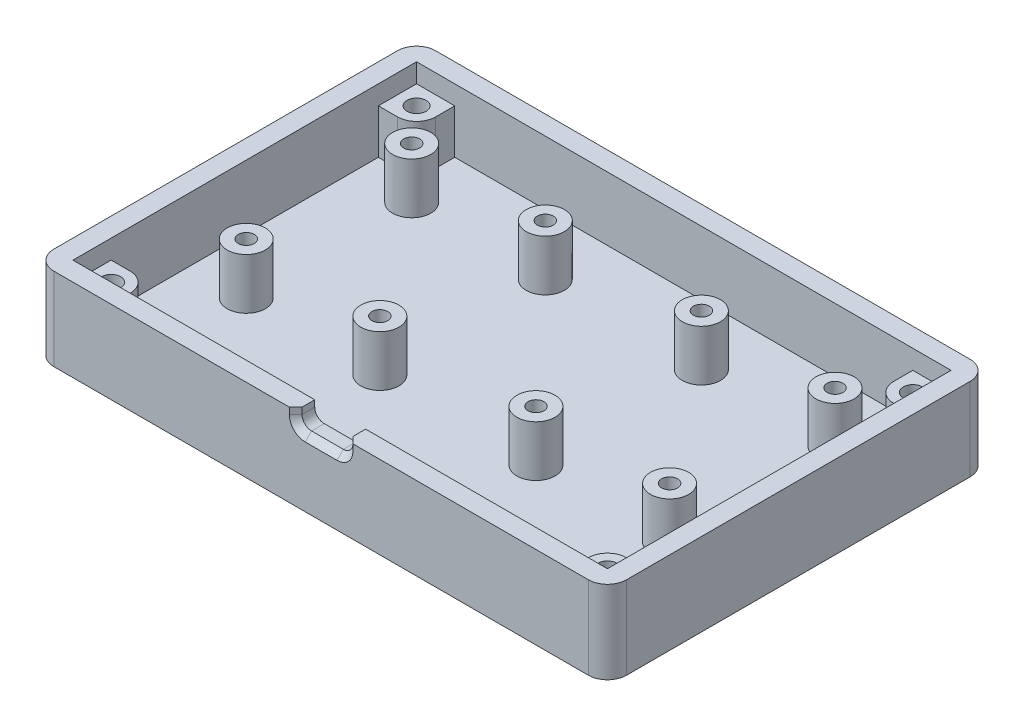
SolidWorks part; units mm, degrees
ref_plane "Спереди" through (0, 0, 0) normal (0, 0, 1) x (1, 0, 0)
ref_plane "Сверху" through (0, 0, 0) normal (0, 1, 0) x (1, 0, 0)
ref_plane "Справа" through (0, 0, 0) normal (1, 0, 0) x (0, 0, -1)
other "Configuration Table"
sketch "Эскиз2" plane through (0, 0, 0) normal (0, 1, 0) x (1, 0, 0)
  line L0 (-48.2034, 25.4414) -> (41.7966, 25.4414)
  line L1 (41.7966, 25.4414) -> (41.7966, -34.5586)
  line L2 (41.7966, -34.5586) -> (-48.2034, -34.5586)
  line L3 (-48.2034, -34.5586) -> (-48.2034, 25.4414)
  dimension "D1" = 90
  dimension "D2" = 60
extrude "Бобышка-Вытянуть1" add sketch "Эскиз2" along normal blind 3
sketch "Эскиз4" plane through (0, 3, 0) normal (0, 1, 0) x (1, 0, 0)
  line L0 (-3.2034, 25.4414) -> (-3.2034, -34.5586) construction
  line L1 (41.7966, 25.4414) -> (-48.2034, 25.4414) construction
  line L2 (-48.2034, -34.5586) -> (41.7966, -34.5586) construction
  line L3 (-48.2034, -4.5586) -> (41.7966, -4.5586) construction
  line L4 (-48.2034, 25.4414) -> (-48.2034, -34.5586) construction
  line L5 (41.7966, -34.5586) -> (41.7966, 25.4414) construction
  line L6 (-38.9685, 15.4414) -> (-12.9685, 15.4414) construction
  line L7 (-12.9685, 15.4414) -> (-12.9685, -18.0586) construction
  line L8 (-12.9685, -18.0586) -> (-38.9685, -18.0586) construction
  line L9 (-38.9685, -18.0586) -> (-38.9685, 15.4414) construction
  line L10 (-42.2034, 19.4414) -> (35.7966, 19.4414) construction
  line L11 (35.7966, 19.4414) -> (35.7966, -28.5586) construction
  line L12 (35.7966, -28.5586) -> (-42.2034, -28.5586) construction
  line L13 (-42.2034, -28.5586) -> (-42.2034, 19.4414) construction
  line L14 (32.5616, -18.0586) -> (32.5616, 15.4414) construction
  line L15 (6.5616, -18.0586) -> (32.5616, -18.0586) construction
  line L16 (6.5616, 15.4414) -> (6.5616, -18.0586) construction
  line L17 (32.5616, 15.4414) -> (6.5616, 15.4414) construction
  line L18 (-25.9685, 15.4414) -> (-25.9685, -18.0586) construction
  line L19 (-38.9685, -0.0586) -> (-12.9685, -0.0586) construction
  circle A0 centre (-36.4685, 12.9414) radius 3
  circle A1 centre (-36.4685, 12.9414) radius 1.25
  circle A2 centre (-15.4685, 12.9414) radius 1.25
  circle A3 centre (-15.4685, 12.9414) radius 3
  circle A4 centre (-15.4685, -13.0586) radius 3
  circle A5 centre (-15.4685, -13.0586) radius 1.25
  circle A6 centre (-36.4685, -13.0586) radius 1.25
  circle A7 centre (-36.4685, -13.0586) radius 3
  circle A8 centre (9.0616, -13.0586) radius 1.25
  circle A9 centre (9.0616, -13.0586) radius 3
  circle A10 centre (30.0616, -13.0586) radius 3
  circle A11 centre (30.0616, -13.0586) radius 1.25
  circle A12 centre (9.0616, 12.9414) radius 3
  circle A13 centre (9.0616, 12.9414) radius 1.25
  circle A14 centre (30.0616, 12.9414) radius 1.25
  circle A15 centre (30.0616, 12.9414) radius 3
  dimension "D10" = 6
  dimension "D11" = 2.5
  dimension "D1" = 6
  dimension "D2" = 6
  dimension "D3" = 6
  dimension "D4" = 6
  dimension "D5" = 26
  dimension "D6" = 33.5
  dimension "D7" = 20
  dimension "D8" = 2.5
  dimension "D9" = 2.5
  dimension "D12" = 13
  dimension "D13" = 5
  dimension "D14" = 13
extrude "Бобышка-Вытянуть2" add sketch "Эскиз4" along normal blind 8
sketch "Эскиз5" plane through (0, 3, 0) normal (0, 1, 0) x (1, 0, 0)
  line L0 (-45.2034, 22.4414) -> (-45.2034, -31.5586)
  line L1 (-45.2034, -31.5586) -> (38.7966, -31.5586)
  line L2 (38.7966, -31.5586) -> (38.7966, 22.4414)
  line L3 (38.7966, 22.4414) -> (-45.2034, 22.4414)
  line L4 (41.7966, 25.4414) -> (-48.2034, 25.4414) construction
  line L5 (-48.2034, 25.4414) -> (-48.2034, -34.5586) construction
  line L6 (-48.2034, -34.5586) -> (41.7966, -34.5586) construction
  line L7 (41.7966, -34.5586) -> (41.7966, 25.4414) construction
  line L9 (-48.2034, 25.4414) -> (41.7966, 25.4414)
  line L10 (-48.2034, 25.4414) -> (-48.2034, -34.5586)
  line L11 (-48.2034, -34.5586) -> (41.7966, -34.5586)
  line L12 (41.7966, 25.4414) -> (41.7966, -34.5586)
  dimension "D1" = 3
  dimension "D2" = 3
  dimension "D3" = 3
  dimension "D4" = 3
extrude "Бобышка-Вытянуть3" add sketch "Эскиз5" along normal blind 10
sketch "Эскиз7" plane through (0, 3, 0) normal (0, 1, 0) x (1, 0, 0)
  line L0 (-39.2034, 19.4414) -> (-39.2034, 22.4414)
  line L1 (38.7966, 22.4414) -> (-45.2034, 22.4414) construction
  line L2 (-42.2034, 16.4414) -> (-45.2034, 16.4414)
  line L3 (-45.2034, 22.4414) -> (-45.2034, -31.5586) construction
  line L4 (-45.2034, 16.4414) -> (-45.2034, 22.4414)
  line L5 (-45.2034, 22.4414) -> (-39.2034, 22.4414)
  line L6 (-3.2034, 22.4414) -> (-3.2034, -31.5586) construction
  line L7 (38.7966, 22.4414) -> (-45.2034, 22.4414) construction
  line L8 (-45.2034, -31.5586) -> (38.7966, -31.5586) construction
  line L9 (-45.2034, -4.5586) -> (38.7966, -4.5586) construction
  line L10 (38.7966, -31.5586) -> (38.7966, 22.4414) construction
  line L11 (38.7966, 22.4414) -> (32.7966, 22.4414)
  line L12 (38.7966, 16.4414) -> (38.7966, 22.4414)
  line L13 (35.7966, 16.4414) -> (38.7966, 16.4414)
  line L14 (32.7966, 19.4414) -> (32.7966, 22.4414)
  line L15 (32.7966, -28.5586) -> (32.7966, -31.5586)
  line L16 (35.7966, -25.5586) -> (38.7966, -25.5586)
  line L17 (38.7966, -25.5586) -> (38.7966, -31.5586)
  line L18 (38.7966, -31.5586) -> (32.7966, -31.5586)
  line L19 (-45.2034, -31.5586) -> (-39.2034, -31.5586)
  line L20 (-45.2034, -25.5586) -> (-45.2034, -31.5586)
  line L21 (-42.2034, -25.5586) -> (-45.2034, -25.5586)
  line L22 (-39.2034, -28.5586) -> (-39.2034, -31.5586)
  arc A0 (-42.2034, 16.4414) -> (-39.2034, 19.4414) centre (-42.2034, 19.4414) ccw
  circle A1 centre (-42.2034, 19.4414) radius 1.5
  circle A2 centre (35.7966, 19.4414) radius 1.5
  arc A3 (35.7966, 16.4414) -> (32.7966, 19.4414) centre (35.7966, 19.4414) cw
  arc A4 (35.7966, -25.5586) -> (32.7966, -28.5586) centre (35.7966, -28.5586) ccw
  circle A5 centre (35.7966, -28.5586) radius 1.5
  circle A6 centre (-42.2034, -28.5586) radius 1.5
  arc A7 (-42.2034, -25.5586) -> (-39.2034, -28.5586) centre (-42.2034, -28.5586) cw
  dimension "D1" = 3
  dimension "D2" = 3
extrude "Бобышка-Вытянуть4" add sketch "Эскиз7" along normal blind 7
sketch "Эскиз8" plane through (0, 3, 0) normal (0, 1, 0) x (1, 0, 0)
  circle A2 centre (-42.2034, 19.4414) radius 1.5
  circle A3 centre (35.7966, 19.4414) radius 1.5
  circle A4 centre (35.7966, -28.5586) radius 1.5
  circle A5 centre (-42.2034, -28.5586) radius 1.5
extrude "Вырез-Вытянуть1" cut sketch "Эскиз8" against normal blind 7 and the other way blind 7
chamfer "Фаска1" distance 2.5 angle 45 4 edges at (-42.2034, 0, 27.0586) (-42.2034, 0, -20.9414) (35.7966, 0, -20.9414) (35.7966, 0, 27.0586)
fillet "Скругление1" radius 3 4 edges at (41.7966, 6.5, -25.4414) (-48.2034, 6.5, -25.4414) (-48.2034, 6.5, 34.5586) (41.7966, 6.5, 34.5586)
sketch "Эскиз9" plane through (0, 0, 34.5586) normal (0, 0, 1) x (1, 0, 0)
  line L0 (-45.2034, 13) -> (38.7966, 13) construction
  line L1 (-5.7034, 15.5) -> (-0.7034, 15.5)
  line L2 (-7.2034, 14) -> (-7.2034, 12)
  line L3 (-5.7034, 10.5) -> (-0.7034, 10.5)
  line L4 (0.7966, 14) -> (0.7966, 12)
  line L5 (-7.2034, 15.5) -> (0.7966, 10.5) construction
  line L6 (-7.2034, 10.5) -> (0.7966, 15.5) construction
  arc A0 (-7.2034, 12) -> (-5.7034, 10.5) centre (-5.7034, 12) ccw
  arc A1 (-0.7034, 10.5) -> (0.7966, 12) centre (-0.7034, 12) ccw
  arc A2 (-0.7034, 15.5) -> (0.7966, 14) centre (-0.7034, 14) cw
  arc A3 (-5.7034, 15.5) -> (-7.2034, 14) centre (-5.7034, 14) ccw
  point P0 (-3.2034, 13)
  dimension "D3" = 1.5
  dimension "D1" = 5
  dimension "D2" = 8
extrude "Вырез-Вытянуть2" cut sketch "Эскиз9" against normal blind 9
chamfer "Фаска2" distance 1 angle 45 5 edges at (-7.2034, 12.5, 34.5586) (-6.7641, 10.9393, 34.5586) (-3.2034, 10.5, 34.5586) (0.7966, 12.5, 34.5586) (0.3572, 10.9393, 34.5586)
